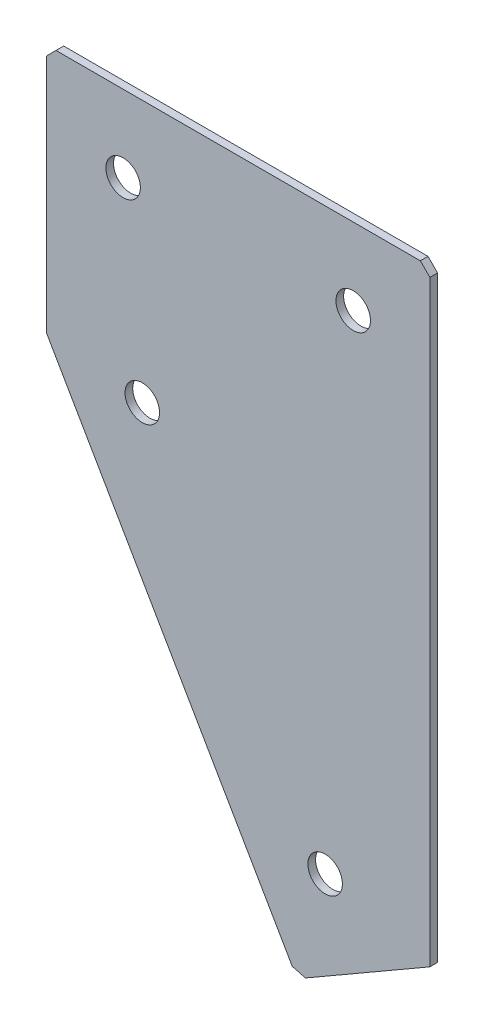
SolidWorks part; units mm, degrees
material "Простая углеродистая сталь"
ref_plane "Спереди" through (0, 0, 0) normal (0, 0, 1) x (1, 0, 0)
ref_plane "Сверху" through (0, 0, 0) normal (0, 1, 0) x (1, 0, 0)
ref_plane "Справа" through (0, 0, 0) normal (1, 0, 0) x (0, 0, -1)
sketch "Эскиз3" plane through (0, 0, 0) normal (0, 0, -1) x (1, 0, 0)
  line L0 (0, 0) -> (100, 0)
  line L1 (100, 0) -> (100, 158.2051)
  line L2 (0, 0) -> (0, 65)
  line L3 (0, 65) -> (65.359, 178.2051)
  line L4 (65.359, 178.2051) -> (100, 158.2051)
  dimension "D1" = 100
  dimension "D2" = 65
  dimension "D3" = 40
  dimension "D4" = 60
  dimension "D5" = 158.2051
extrude "Бобышка-Вытянуть1" add sketch "Эскиз3" along normal blind 2
hole_wizard "Отверстие с зазором M81" positions "Эскиз4" profile "Эскиз5" hole size "M8" standard "DIN" end condition through all
sketch "Эскиз4" plane through (0, 0, -2) normal (0, 0, -1) x (1, 0, 0)
  line L0 (25, 68.3013) -> (72.6795, 150.8846) construction
  line L2 (65.359, 178.2051) -> (0, 65) construction
  line L3 (20, 20) -> (80, 20) construction
  line L5 (0, 0) -> (100, 0) construction
  line L6 (0, 65) -> (0, 0) construction
  line L7 (100, 0) -> (100, 158.2051) construction
  line L8 (100, 158.2051) -> (65.359, 178.2051) construction
  line L9 (25, 68.3013) -> (0, 25) construction
  point P0 (20, 20)
  point P2 (80, 20)
  point P4 (25, 68.3013)
  point P6 (72.6795, 150.8846)
  dimension "D1" = 20
  dimension "D2" = 20
  dimension "D3" = 20
  dimension "D4" = 20
  dimension "D5" = 20
  dimension "D6" = 50
  dimension "D7" = 95.359
  dimension "D8" = 60
sketch "Эскиз5" plane through (20, -20, -2) normal (1, 0, 0) x (0, 1, 0)
  line L0 (0, 0) -> (0, 2)
  line L1 (0, 2) -> (4.5, 2)
  line L2 (4.5, 2) -> (4.5, 0)
  line L5 (4.5, 0) -> (0, 0)
  line L11 (0, -6.35) -> (0, 107.95) construction
  dimension "Диаметр сквозного отверстия" = 9
  dimension "Глубина сквозного отверстия" = 2
chamfer "Фаска1" distance 2.5 distance2 2.5 3 edges at (65.359, -178.2051, -1) (100, 0, -1) (0, 0, -1)
